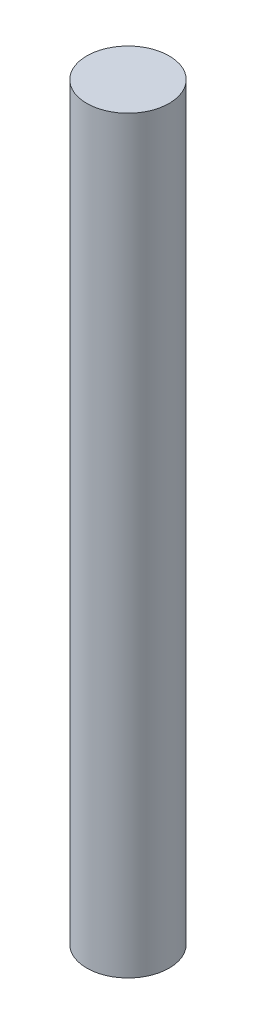
SolidWorks part; units mm, degrees
ref_plane "Front" through (0, 0, 0) normal (0, 0, 1) x (1, 0, 0)
ref_plane "Top" through (0, 0, 0) normal (0, 1, 0) x (1, 0, 0)
ref_plane "Right" through (0, 0, 0) normal (1, 0, 0) x (0, 0, -1)
sketch "Sketch1" plane through (0, 0, 0) normal (0, 1, 0) x (1, 0, 0)
  circle A0 centre (0, 0) radius 2.794
  dimension "D1" = 5.588
extrude "Boss-Extrude1" add sketch "Sketch1" along normal blind 50.8
